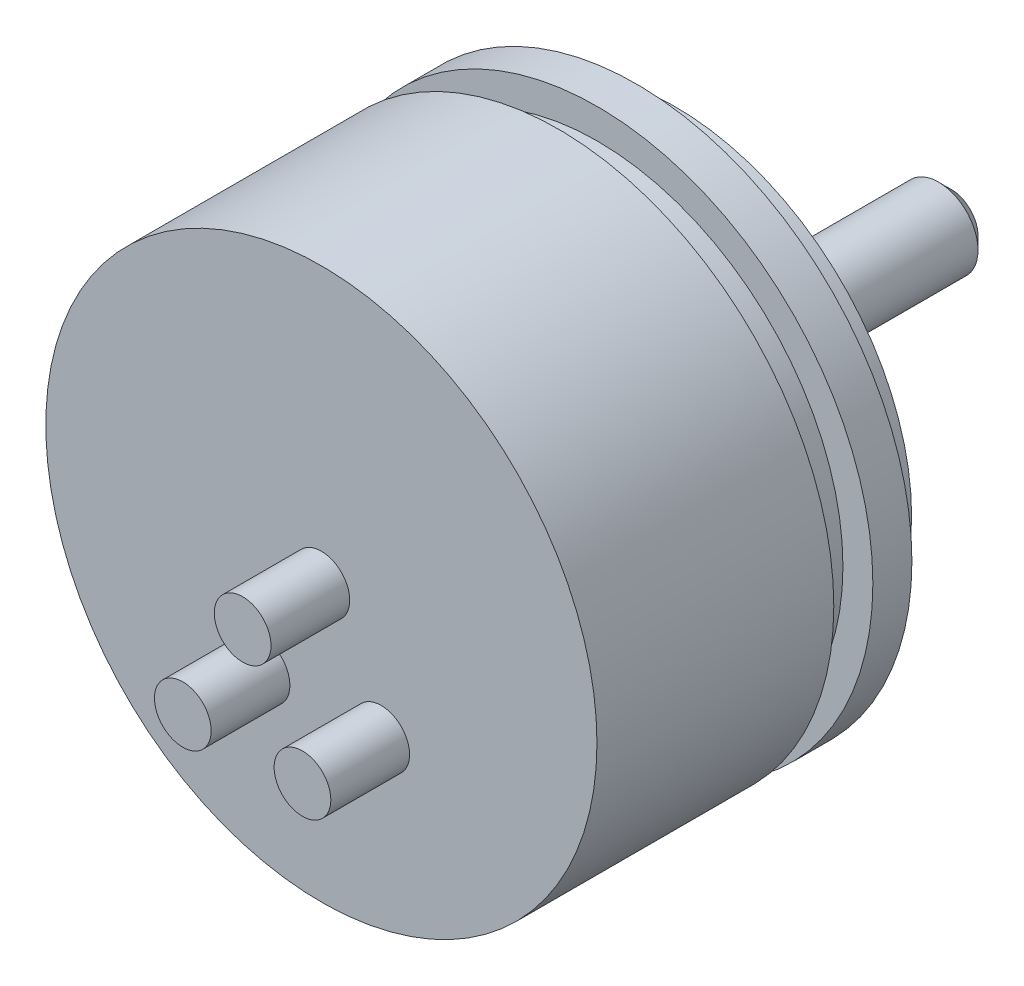
SolidWorks part; units mm, degrees
ref_plane "Front Plane" through (0, 0, 0) normal (0, 0, 1) x (1, 0, 0)
ref_plane "Top Plane" through (0, 0, 0) normal (0, 1, 0) x (1, 0, 0)
ref_plane "Right Plane" through (0, 0, 0) normal (1, 0, 0) x (0, 0, -1)
sketch "Sketch2" plane through (0, 0, 0) normal (1, 0, 0) x (0, 0, -1)
  line L0 (-9.5504, 0) -> (-9.5504, 11.1125)
  line L1 (55, 0) -> (-55, 0) construction
  line L2 (-9.5504, 11.1125) -> (0, 11.1125)
  line L3 (0, 55) -> (0, -55) construction
  line L4 (0, 11.1125) -> (0, 9.906)
  line L5 (0, 9.906) -> (1.5748, 9.906)
  line L6 (1.5748, 9.906) -> (1.5748, 11.1125)
  line L7 (1.5748, 11.1125) -> (3.1496, 11.1125)
  line L8 (3.1496, 11.1125) -> (3.1496, 9.525)
  line L9 (3.1496, 9.525) -> (4.7244, 9.525)
  line L10 (4.7244, 9.525) -> (4.7244, 0)
  line L11 (-28.0408, 0) -> (34.2323, 0) construction
  line L12 (4.7244, 1.839) -> (5.2324, 1.839)
  line L13 (5.2324, 1.585) -> (15.3416, 1.585)
  line L14 (15.3416, 1.585) -> (15.8496, 1.077)
  line L15 (15.8496, 1.077) -> (15.8496, 0)
  line L16 (5.2324, 1.839) -> (5.2324, 1.585)
  dimension "D1" = 22.225
  dimension "D2" = 1.5748
  dimension "D3" = 1.5748
  dimension "D4" = 1.5748
  dimension "D5" = 12.7
  dimension "D6" = 19.812
  dimension "D7" = 19.05
  dimension "D8" = 12.7
  dimension "D9" = 3.1699
  dimension "D10" = 0.508
  dimension "D11" = 45
  dimension "D12" = 0.508
  dimension "D13" = 0.254
revolve "Revolve2" add sketch "Sketch2" angle 360 about L11
sketch "Sketch3" plane through (0, 0, 9.5504) normal (0, 0, 1) x (1, 0, 0)
  line L0 (0, 0) -> (-2.413, -4.1794) construction
  line L1 (0, 0) -> (2.413, -4.1794) construction
  line L2 (0, -12.2237) -> (0, 12.2237) construction
  circle A0 centre (0, 0) radius 1.143
  circle A1 centre (-2.413, -4.1794) radius 1.143
  circle A2 centre (2.413, -4.1794) radius 1.143
  dimension "D3" = 4.826
  dimension "D4" = 2.286
  dimension "D1" = 60
  dimension "D2" = 30
extrude "Boss-Extrude1" add sketch "Sketch3" along normal blind 3.175
